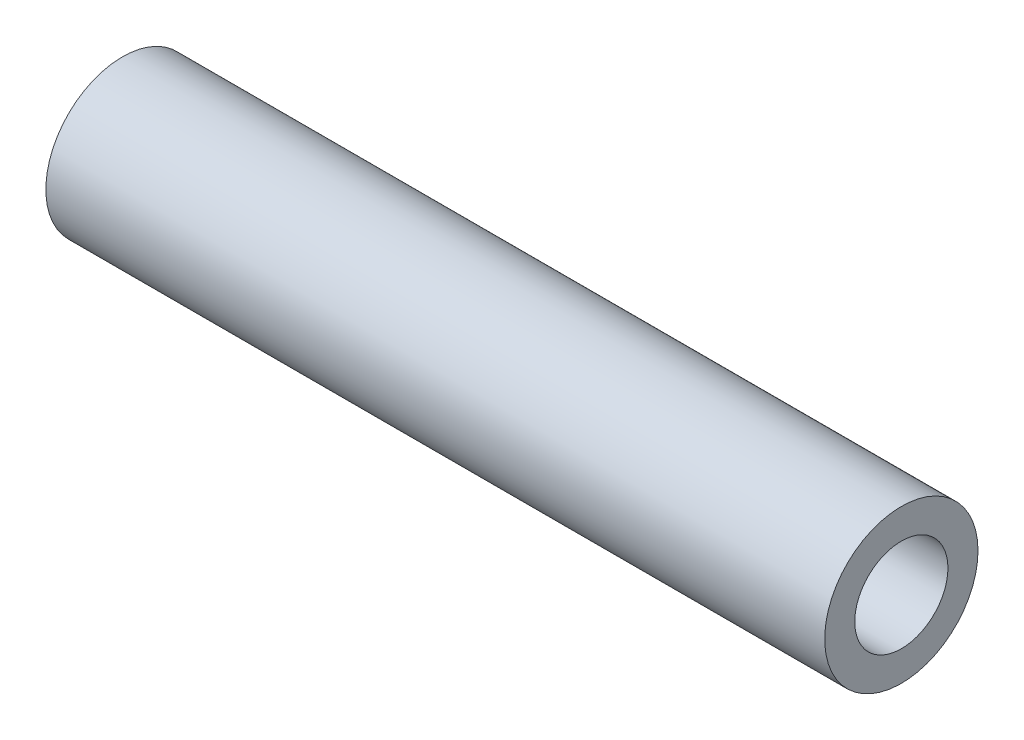
SolidWorks part; units mm, degrees
material "6061-T6 (SS)"
ref_plane "Front" through (0, 0, 0) normal (0, 0, 1) x (1, 0, 0)
ref_plane "Top" through (0, 0, 0) normal (0, 1, 0) x (1, 0, 0)
ref_plane "Right" through (0, 0, 0) normal (1, 0, 0) x (0, 0, -1)
sketch "Sketch1" plane through (0, 0, 0) normal (1, 0, 0) x (0, 0, -1)
  circle A0 centre (0, 0) radius 1.9304
  circle A1 centre (0, 0) radius 3.175
  dimension "D1" = 1.2446
  dimension "D2" = 6.35
extrude "Boss-Extrude1" add sketch "Sketch1" along normal mid plane 32.258
